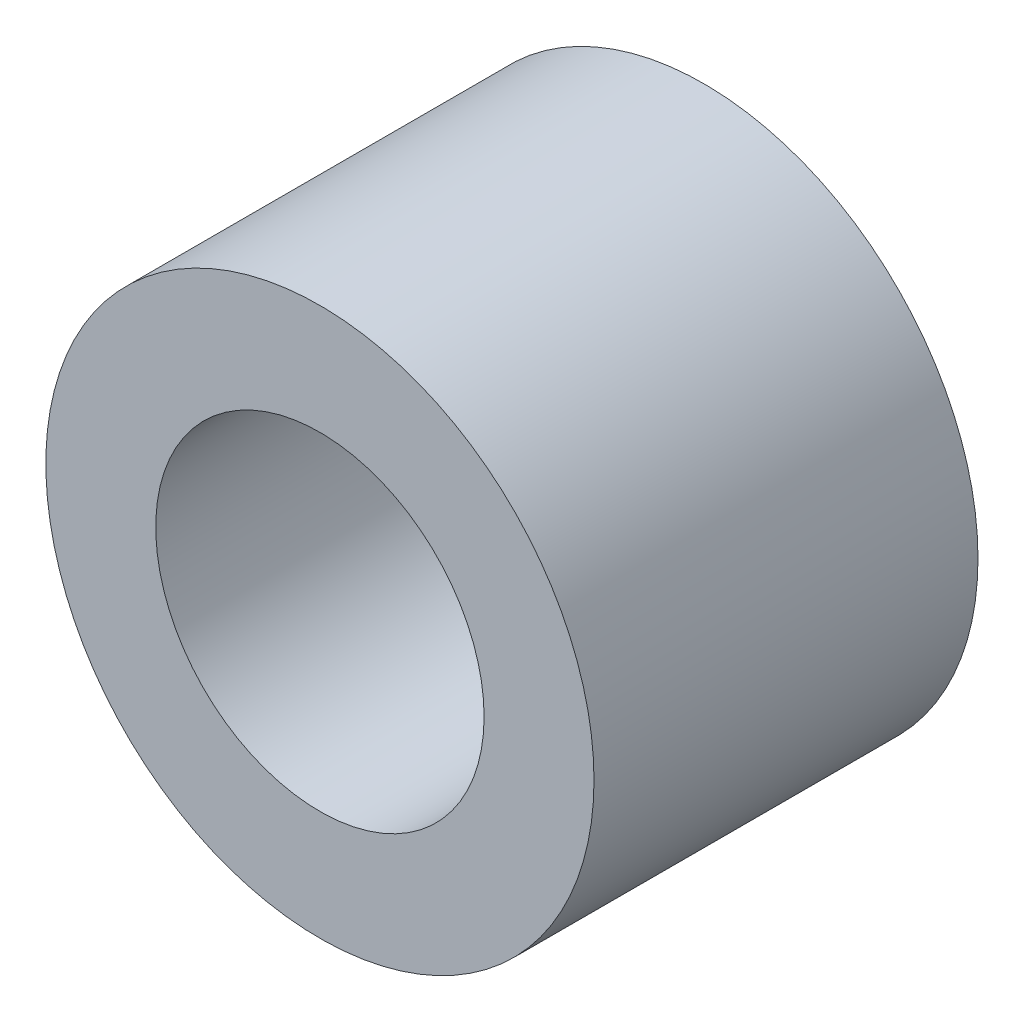
SolidWorks part; units mm, degrees
ref_plane "Front Plane" through (0, 0, 0) normal (0, 0, 1) x (1, 0, 0)
ref_plane "Top Plane" through (0, 0, 0) normal (0, 1, 0) x (1, 0, 0)
ref_plane "Right Plane" through (0, 0, 0) normal (1, 0, 0) x (0, 0, -1)
sketch "Sketch1" plane through (0, 0, 0) normal (0, 0, 1) x (1, 0, 0)
  circle A0 centre (0, 0) radius 2.6289
  circle A1 centre (0, 0) radius 1.5748
  dimension "D1" = 5.2578
  dimension "D2" = 3.1496
extrude "Boss-Extrude1" add sketch "Sketch1" along normal blind 3.683
